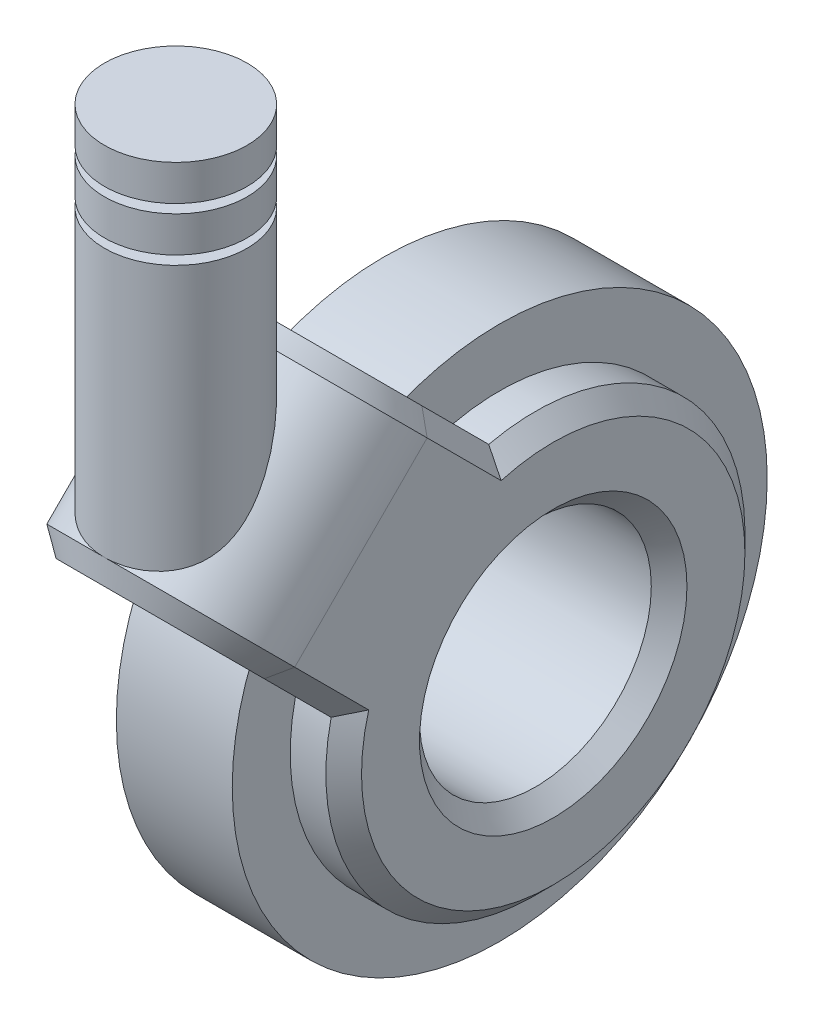
SolidWorks part; units mm, degrees
ref_plane "Front Plane" through (0, 0, 0) normal (0, 0, 1) x (1, 0, 0)
ref_plane "Top Plane" through (0, 0, 0) normal (0, 1, 0) x (1, 0, 0)
ref_plane "Right Plane" through (0, 0, 0) normal (1, 0, 0) x (0, 0, -1)
sketch "Sketch1" plane through (0, 0, 0) normal (1, 0, 0) x (0, 0, -1)
  circle A0 centre (0, 0) radius 13.5
  circle A1 centre (0, 0) radius 30
  dimension "D1" = 60
  dimension "D2" = 27
extrude "Boss-Extrude1" add sketch "Sketch1" along normal mid plane 13
sketch "Sketch2" plane through (0, 0, 0) normal (1, 0, 0) x (0, 0, -1)
  circle A0 centre (0, 0) radius 13
  circle A1 centre (0, 0) radius 23.5
  dimension "D1" = 47
  dimension "D2" = 26
extrude "Boss-Extrude2" add sketch "Sketch2" along normal mid plane 25 separate body
ref_plane "Plane1" through (0, 0, 0) normal (0, 0.7071, -0.7071) x (-1, 0, 0)
sketch "Sketch4" plane through (0, 0, 0) normal (0, 0.7071, -0.7071) x (-1, 0, 0)
  line L0 (-12.5, 18.5) -> (-12.5, 30.5)
  line L1 (12.5, 18.5) -> (12.5, 30.5)
  line L3 (-12.5, 18.5) -> (-7.5, 18.5)
  line L4 (-7.5, 18.5) -> (-7.5, 30.5)
  line L5 (12.5, 18.5) -> (7.5, 18.5)
  line L7 (7.5, 18.5) -> (7.5, 30.5)
  line L8 (6.5, 30) -> (-6.5, 30) construction
  line L10 (12.5, -23.5) -> (12.5, 23.5) construction
  line L11 (-12.5, 23.5) -> (-12.5, -23.5) construction
  line L12 (12.5, 23.5) -> (-12.5, 23.5) construction
  line L13 (12.5, 23.5) -> (-12.5, 23.5) construction
  arc A0 (12.5, 30.5) -> (-12.5, 30.5) centre (0, 30.5) ccw
  arc A1 (7.5, 30.5) -> (-7.5, 30.5) centre (0, 30.5) ccw
  point P16 (0, 38)
  point P17 (0, 43)
  dimension "D1" = 5
  dimension "D2" = 5
  dimension "D3" = 5
  dimension "D4" = 13
  dimension "D5" = 5
  dimension "D6" = 5
extrude "Boss-Extrude3" add sketch "Sketch4" along normal mid plane 25
chamfer "Chamfer1" distance 2 angle 45 10 edges at (-12.5, 0, -13) (-12.5, 26.6578, 8.9802) (-12.5, 8.9802, 26.6578) (-12.5, -16.617, -16.617) (12.5, 0, -13) (0, 21.5668, 39.2444) (0, 39.2444, 21.5668) (12.5, 8.9802, 26.6578) (12.5, 26.6578, 8.9802) (12.5, -16.617, -16.617)
ref_plane "Plane2" through (0, 53, 0) normal (0, 1, 0) x (1, 0, 0)
sketch "Sketch5" plane through (0, 53, 0) normal (0, 1, 0) x (1, 0, 0)
  line L0 (0, -55) -> (0, 55) construction
  circle A0 centre (0, -29.8302) radius 8
  ellipse E0 centre (0, -28.9914) end of major axis (12.5, -28.9914) minor radius 8.8388 (-12.5, -28.9914) -> (12.5, -28.9914) ccw construction
  ellipse E1 centre (0, -28.9914) end of major axis (12.5, -28.9914) minor radius 8.8388 (-12.5, -28.9914) -> (12.5, -28.9914) ccw construction
  dimension "D1" = 16
extrude "Boss-Extrude4" add sketch "Sketch5" against normal up to next contours A0
sketch "Sketch6" plane through (0, 0, 0) normal (1, 0, 0) x (0, 0, -1)
  line L0 (-29.8302, 53) -> (-29.8302, 63)
  line L1 (-21.8302, 53) -> (-37.8302, 53) construction
  line L2 (-29.8302, 63) -> (-21.8302, 63)
  line L3 (-21.8302, 63) -> (-21.8302, 59)
  line L4 (-21.8302, 59) -> (-23.8302, 59)
  line L5 (-23.8302, 59) -> (-23.8302, 58)
  line L6 (-23.8302, 58) -> (-21.8302, 58)
  line L7 (-21.8302, 58) -> (-21.8302, 54)
  line L8 (-21.8302, 54) -> (-23.8302, 54)
  line L9 (-23.8302, 54) -> (-23.8302, 53)
  line L10 (-23.8302, 53) -> (-29.8302, 53)
  dimension "D1" = 2
  dimension "D2" = 1
  dimension "D3" = 1
  dimension "D4" = 4
  dimension "D5" = 10
revolve "Revolve1" add sketch "Sketch6" angle 360 about L0
